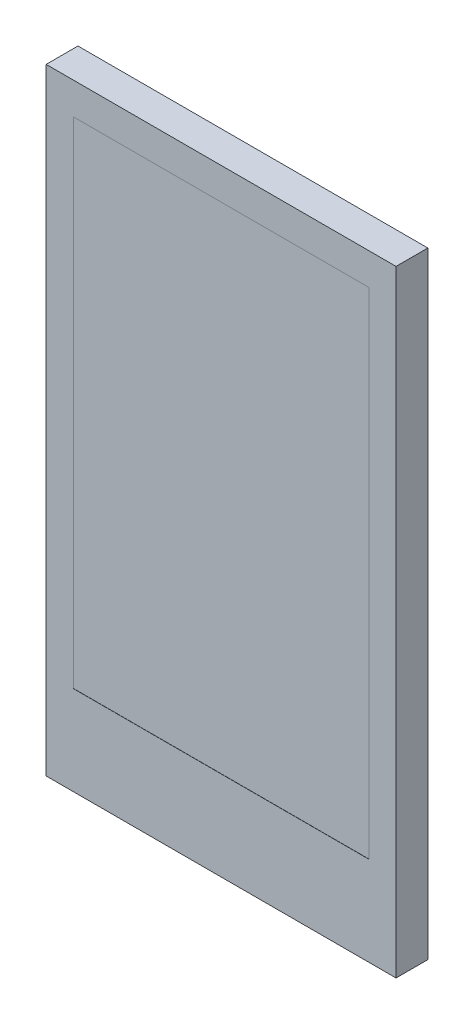
SolidWorks part; units mm, degrees
ref_plane "前视基准面" through (0, 0, 0) normal (0, 0, 1) x (1, 0, 0)
ref_plane "上视基准面" through (0, 0, 0) normal (0, 1, 0) x (1, 0, 0)
ref_plane "右视基准面" through (0, 0, 0) normal (1, 0, 0) x (0, 0, -1)
sketch "草图1" plane through (0, 0, 0) normal (0, 0, 1) x (1, 0, 0)
  line L1 (8.8, -15.5) -> (-8.8, -15.5)
  line L2 (8.8, -15.5) -> (8.8, 15.5)
  line L3 (8.8, 15.5) -> (-8.8, 15.5)
  line L4 (-8.8, -15.5) -> (-8.8, 15.5)
  line L5 (8.8, -15.5) -> (-8.8, 15.5) construction
  line L6 (8.8, 15.5) -> (-8.8, -15.5) construction
  point P0 (0, 0)
extrude "凸台-拉伸1" add sketch "草图1" along normal blind 1.6
sketch "草图2" plane through (0, 0, 1.6) normal (0, 0, 1) x (1, 0, 0)
  line L0 (0, 15.5) -> (0, 13.9) construction
  line L9 (8.8, 15.5) -> (-8.8, 15.5) construction
  line L10 (7.43, 13.9) -> (-7.43, 13.9)
  line L11 (-7.43, 13.9) -> (-7.43, -11.01)
  line L12 (-7.43, -11.01) -> (7.43, -11.01)
  line L13 (7.43, -11.01) -> (7.43, 13.9)
  point P7 (0, 13.9)
extrude "切除-拉伸1" cut sketch "草图2" against normal blind 0.01
